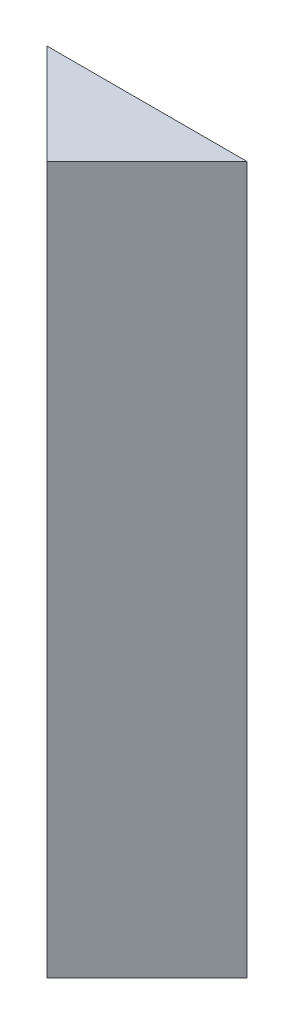
SolidWorks part; units mm, degrees
ref_plane "前视基准面" through (0, 0, 0) normal (0, 0, 1) x (1, 0, 0)
ref_plane "上视基准面" through (0, 0, 0) normal (0, 1, 0) x (1, 0, 0)
ref_plane "右视基准面" through (0, 0, 0) normal (1, 0, 0) x (0, 0, -1)
sketch "草图1" plane through (0, 0, 0) normal (0, 1, 0) x (1, 0, 0)
  line L0 (0, 0) -> (2.1213, -2.1213)
  line L1 (2.1213, -2.1213) -> (4.2426, 0)
  line L2 (4.2426, 0) -> (0, 0)
  dimension "D1" = 3
  dimension "D2" = 3
extrude "凸台-拉伸1" add sketch "草图1" along normal blind 15
